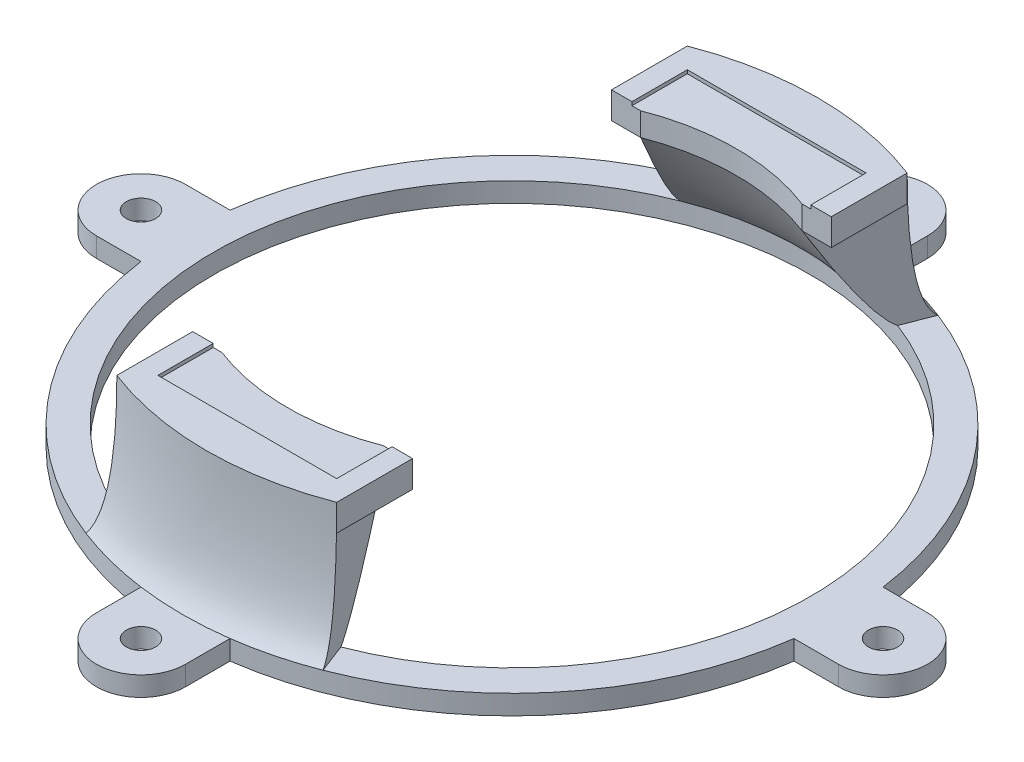
SolidWorks part; units mm, degrees
ref_plane "Front Plane" through (0, 0, 0) normal (0, 0, 1) x (1, 0, 0)
ref_plane "Top Plane" through (0, 0, 0) normal (0, 1, 0) x (1, 0, 0)
ref_plane "Right Plane" through (0, 0, 0) normal (1, 0, 0) x (0, 0, -1)
sketch "Sketch1" plane through (0, 0, 0) normal (0, 1, 0) x (1, 0, 0)
  line L0 (0, -6.35) -> (0, 6.35) construction
  line L1 (0, 6.35) -> (46.559, 6.35) construction
  line L2 (0, -6.35) -> (46.559, -6.35) construction
  line L3 (46.559, 6.35) -> (52.909, 6.35)
  line L4 (46.559, -6.35) -> (52.909, -6.35)
  line L5 (6.35, -46.559) -> (6.35, -52.909)
  line L6 (-6.35, -46.559) -> (-6.35, -52.909)
  line L7 (-46.559, -6.35) -> (-52.909, -6.35)
  line L8 (-46.559, 6.35) -> (-52.909, 6.35)
  line L9 (-6.35, 46.559) -> (-6.35, 52.909)
  line L10 (6.35, 46.559) -> (6.35, 52.909)
  arc A0 (46.559, 6.35) -> (6.35, 46.559) centre (0, 0) ccw
  arc A1 (52.909, 6.35) -> (52.909, -6.35) centre (52.909, 0) cw
  arc A2 (6.35, -52.909) -> (-6.35, -52.909) centre (0, -52.909) cw
  arc A3 (-52.909, -6.35) -> (-52.909, 6.35) centre (-52.909, 0) cw
  arc A4 (-6.35, 52.909) -> (6.35, 52.909) centre (0, 52.909) cw
  arc A5 (-6.35, 46.559) -> (-46.559, 6.35) centre (0, 0) ccw
  arc A6 (-46.559, -6.35) -> (-6.35, -46.559) centre (0, 0) ccw
  arc A7 (6.35, -46.559) -> (46.559, -6.35) centre (0, 0) ccw
  circle A8 centre (52.909, 0) radius 2.0955
  circle A9 centre (0, -52.909) radius 2.0955
  circle A10 centre (-52.909, 0) radius 2.0955
  circle A11 centre (0, 52.909) radius 2.0955
  point P5 (0, 0)
  point P29 (0, 0)
  point P36 (0, 0)
  dimension "D1" = 93.98
  dimension "D6" = 4.191
  dimension "D2" = 12.7
  dimension "D3" = 6.35
  dimension "D4" = 6.35
  dimension "D5" = 4
  dimension "D7" = 4
extrude "Boss-Extrude1" add sketch "Sketch1" along normal blind 2.794
sketch "Sketch2" plane through (0, 2.794, 0) normal (0, 1, 0) x (1, 0, 0)
  circle A0 centre (0, 0) radius 42.545
  arc A1 (46.559, 6.35) -> (6.35, 46.559) centre (0, 0) ccw construction
  dimension "D1" = 85.09
extrude "Cut-Extrude2" cut sketch "Sketch2" against normal through all
sketch "Sketch3" plane through (0, 2.794, 0) normal (0, 1, 0) x (1, 0, 0)
  circle A0 centre (0, 0) radius 44.45
  circle A1 centre (0, 0) radius 42.545 construction
  circle A2 centre (0, 0) radius 46.99
  arc A3 (46.559, 6.35) -> (6.35, 46.559) centre (0, 0) ccw construction
  dimension "D1" = 88.9
extrude "Boss-Extrude2" [suppressed] add sketch "Sketch3" along normal blind 3.81
ref_plane "Print_Plane" through (0, 21.336, 0) normal (0, -1, 0) x (-1, 0, 0)
sketch "Sketch4" plane through (0, 21.336, 0) normal (0, -1, 0) x (-1, 0, 0)
  line L0 (-12.5, 0) -> (12.5, 0) construction
  line L1 (-12.5, -37.5) -> (12.5, -37.5) construction
  line L2 (-12.5, -37.5) -> (-12.5, 37.5) construction
  line L3 (-12.5, 37.5) -> (12.5, 37.5) construction
  line L4 (12.5, -37.5) -> (12.5, 37.5) construction
  line L5 (-15.675, -40.675) -> (-15.675, 40.675)
  line L6 (-15.675, 40.675) -> (15.675, 40.675)
  line L7 (15.675, -40.675) -> (15.675, 40.675)
  line L8 (-15.675, -40.675) -> (15.675, -40.675)
  circle A0 centre (0, 0) radius 42.545 construction
  point P6 (0, 0)
  dimension "D1" = 75
  dimension "D2" = 25
  dimension "D3" = 3.175
extrude "Boss-Extrude3" add sketch "Sketch4" along normal blind 3.81 separate body
ref_plane "Surface_1_Plane" through (0, 0, 0) normal (0.9331, 0, 0.3596) x (0.3596, 0, -0.9331)
ref_plane "Surface_2_Plane" through (0, 0, 0) normal (0.9331, 0, -0.3596) x (-0.3596, 0, -0.9331)
sketch "Sketch6" plane through (0, 0, 0) normal (0.9331, 0, 0.3596) x (0.3596, 0, -0.9331)
  line L5 (43.5908, 17.526) -> (43.5908, 21.336) construction
  line L9 (42.545, 2.794) -> (-42.545, 2.794) construction
  line L10 (42.545, 2.794) -> (38.735, 5.334) construction
  line L11 (38.735, 5.334) -> (29.845, 21.336) construction
  line L13 (46.99, 2.794) -> (22.6676, 2.794) construction
  line L14 (43.5908, 21.336) -> (43.5908, 5.334) construction
  line L15 (43.5908, 5.334) -> (46.99, 2.794) construction
  line L22 (46.99, 2.794) -> (42.545, 2.794)
  line L23 (43.5908, 21.336) -> (29.845, 21.336)
  spline S0 degree 2 poles (43.5908, 21.336) (43.5908, 5.334) (46.99, 2.794) knots 0 0 0 1 1 1
  spline S1 degree 2 poles (42.545, 2.794) (38.735, 5.334) (29.845, 21.336) knots 0 0 0 1 1 1
  dimension "D1" = 2.54
  dimension "D2" = 2.54
  dimension "D3" = 3.81
  dimension "D4" = 12.7
sketch "Sketch22" plane through (0, 2.794, 0) normal (0, 1, 0) x (1, 0, 0)
  line L0 (3.4662, -8.9945) -> (-3.4662, 8.9945) construction
  arc A0 (15.2989, 39.6991) -> (-15.2989, 39.6991) centre (0, 0) ccw
sweep "Sweep2" add profiles "Sketch6" path "Sketch22"
pattern_circular "CirPattern1" count 2 over 360 of "Sweep2"
sketch "Sketch5" plane through (0, 21.336, 0) normal (0, 1, 0) x (1, 0, 0)
  line L0 (12.75, 0) -> (-12.75, 0) construction
  line L1 (12.75, -37.75) -> (-12.75, -37.75)
  line L2 (12.75, -37.75) -> (12.75, 37.75)
  line L3 (12.75, 37.75) -> (-12.75, 37.75)
  line L4 (-12.75, -37.75) -> (-12.75, 37.75)
  circle A0 centre (0, 0) radius 42.545 construction
  point P6 (0, 0)
  dimension "D1" = 25.5
  dimension "D2" = 75.5
extrude "Cut-Extrude3" cut sketch "Sketch5" against normal blind 0.5
sketch "Sketch24" plane through (0, 17.526, 0) normal (0, -1, 0) x (1, 0, 0)
  line L0 (-15.675, 29.8591) -> (-15.675, -29.8591)
  line L2 (-15.675, 29.8591) -> (15.675, 29.8591)
  line L3 (-15.675, -29.8591) -> (15.675, -29.8591)
  line L4 (15.675, 29.8591) -> (15.675, -29.8591)
  line L5 (-15.675, 29.8591) -> (15.675, -29.8591) construction
  line L6 (-15.675, -29.8591) -> (15.675, 29.8591) construction
  line L8 (15.675, -40.675) -> (15.675, 40.675) construction
  point P1 (0, 0)
extrude "Cut-Extrude5" cut sketch "Sketch24" against normal up to next
sketch "Sketch25" plane through (0, 17.526, 0) normal (0, -1, 0) x (1, 0, 0)
  circle A0 centre (0, 0) radius 31.9996
  arc A1 (-11.5068, -29.8591) -> (11.5068, -29.8591) centre (0, 0) ccw construction
extrude "Cut-Extrude6" cut sketch "Sketch25" against normal up to next
